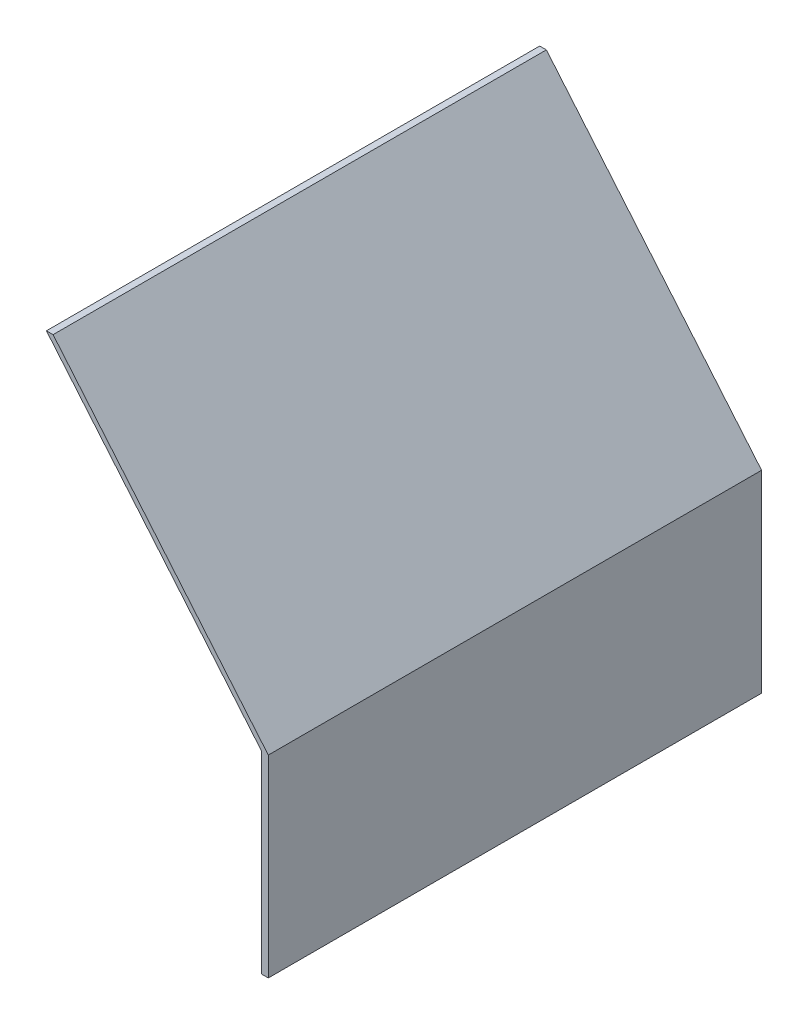
SolidWorks part; units mm, degrees
material "Plain Carbon Steel"
ref_plane "Front Plane" through (0, 0, 0) normal (0, 0, 1) x (1, 0, 0)
ref_plane "Top Plane" through (0, 0, 0) normal (0, 1, 0) x (1, 0, 0)
ref_plane "Right Plane" through (0, 0, 0) normal (1, 0, 0) x (0, 0, -1)
sketch "Sketch1" plane through (0, 0, 0) normal (0, 0, 1) x (1, 0, 0)
  line L0 (0, 0) -> (-1.5189, 0)
  line L1 (-1.5189, 0) -> (-1.5189, 43.942)
  line L2 (-1.5189, 43.942) -> (-50.4993, 102.3146)
  line L3 (-50.4993, 102.3146) -> (-48.9804, 102.3146)
  line L4 (-48.9804, 102.3146) -> (0, 43.942)
  line L5 (0, 43.942) -> (0, 0)
  line L6 (-1.5189, 43.942) -> (0, 43.942) construction
  dimension "D1" = 1.5189
  dimension "D2" = 1.5189
  dimension "D3" = 76.2
  dimension "D4" = 140
  dimension "D5" = 43.942
extrude "Boss-Extrude1" add sketch "Sketch1" along normal blind 112.268
